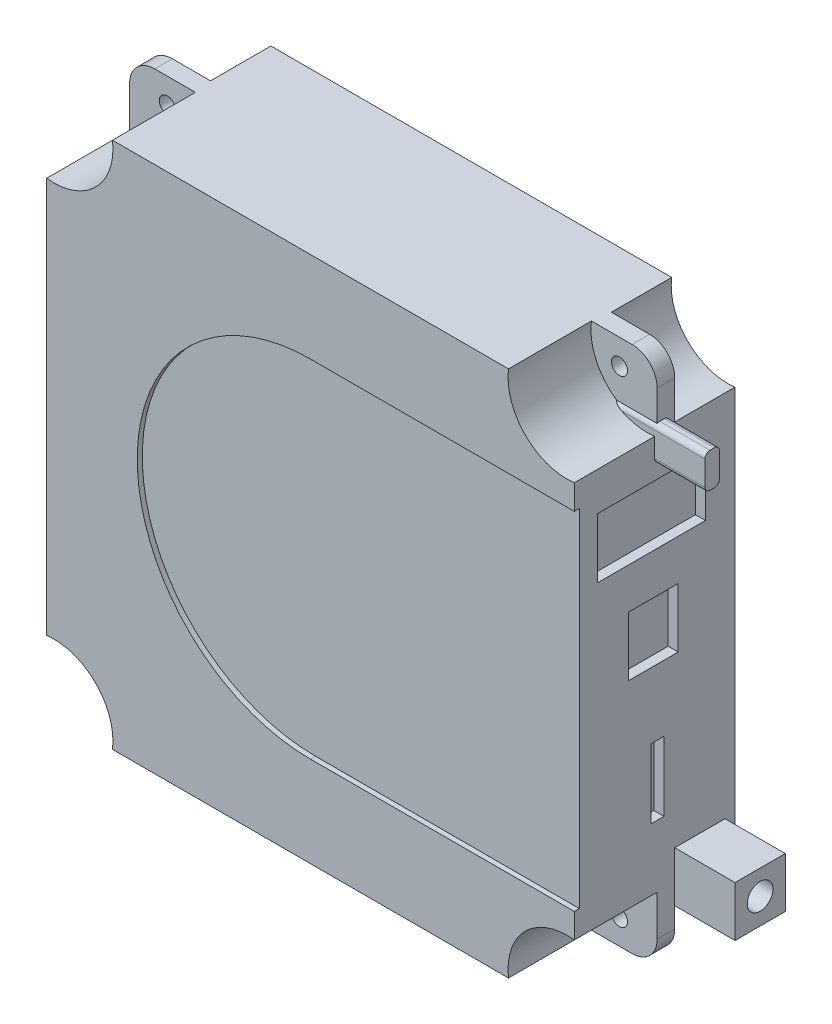
SolidWorks part; units mm, degrees
ref_plane "前视基准面" through (0, 0, 0) normal (0, 0, 1) x (1, 0, 0)
ref_plane "上视基准面" through (0, 0, 0) normal (0, 1, 0) x (1, 0, 0)
ref_plane "右视基准面" through (0, 0, 0) normal (1, 0, 0) x (0, 0, -1)
sketch "草图1" plane through (0, 0, 0) normal (0, 0, 1) x (1, 0, 0)
  line L1 (-47.5, -52.5) -> (47.5, -52.5)
  line L2 (-52.5, -47.5) -> (-52.5, 47.5)
  line L3 (-47.5, 52.5) -> (47.5, 52.5)
  line L4 (52.5, -47.5) -> (52.5, 47.5)
  line L5 (-52.5, -52.5) -> (52.5, 52.5) construction
  line L6 (-52.5, 52.5) -> (52.5, -52.5) construction
  line L7 (-45, -47.5) -> (45, -47.5)
  line L8 (-45, -47.5) -> (-45, 47.5)
  line L9 (-45, 47.5) -> (45, 47.5)
  line L10 (45, -47.5) -> (45, 47.5)
  line L11 (-45, -47.5) -> (45, 47.5) construction
  line L12 (-45, 47.5) -> (45, -47.5) construction
  circle A0 centre (-45, 47.5) radius 1.6
  circle A1 centre (45, 47.5) radius 1.6
  circle A2 centre (-45, -47.5) radius 1.6
  circle A3 centre (45, -47.5) radius 1.6
  arc A4 (52.5, -47.5) -> (47.5, -52.5) centre (47.5, -47.5) cw
  arc A5 (-47.5, -52.5) -> (-52.5, -47.5) centre (-47.5, -47.5) cw
  arc A6 (52.5, 47.5) -> (47.5, 52.5) centre (47.5, 47.5) ccw
  arc A7 (-52.5, 47.5) -> (-47.5, 52.5) centre (-47.5, 47.5) cw
  point P0 (0, 0)
  point P6 (0, 0)
  dimension "D5" = 5
  dimension "D1" = 105
  dimension "D2" = 105
  dimension "D3" = 90
  dimension "D4" = 95
extrude "凸台-拉伸1" add sketch "草图1" along normal blind 32 contours A7 L2 A5 L1 A4 L4 A6 L3 A3 L7 A2 L8 A0 L9 A1 L10 | A3 L10 A1 L9 A0 L8 A2 L7
sketch "草图2" plane through (52.5, 0, 0) normal (1, 0, 0) x (0, 0, -1)
  line L1 (-21.2339, 11.7062) -> (-11.3035, 11.7062)
  line L2 (-21.2339, 11.7062) -> (-21.2339, -0.111)
  line L3 (-21.2339, -0.111) -> (-11.3035, -0.111)
  line L4 (-11.3035, 11.7062) -> (-11.3035, -0.111)
  line L5 (-27.337, 31.7636) -> (-5.8873, 31.7636)
  line L6 (-27.337, 31.7636) -> (-27.337, 19.8471)
  line L7 (-27.337, 19.8471) -> (-5.8873, 19.8471)
  line L8 (-5.8873, 31.7636) -> (-5.8873, 19.8471)
  line L9 (-16.7269, -13.2121) -> (-14.145, -13.2121)
  line L10 (-16.7269, -13.2121) -> (-16.7269, -27.0154)
  line L11 (-16.7269, -27.0154) -> (-14.145, -27.0154)
  line L12 (-14.145, -13.2121) -> (-14.145, -27.0154)
extrude "切除-拉伸1" cut sketch "草图2" against normal blind 2
sketch "草图3" plane through (0, 0, 32) normal (0, 0, 1) x (1, 0, 0)
  circle A0 centre (-51.0355, 51.0355) radius 11.717
  arc A1 (-47.5, 52.5) -> (-52.5, 47.5) centre (-47.5, 47.5) ccw construction
  circle A2 centre (51.0355, 51.0355) radius 11.717
  circle A3 centre (51.0355, -51.0355) radius 11.717
  circle A4 centre (-51.0355, -51.0355) radius 11.717
  point P14 (0, 0)
  dimension "D1" = 4
extrude "切除-拉伸2" cut sketch "草图3" against normal blind 16.5
sketch "草图4" plane through (0, 0, 0) normal (0, 0, -1) x (-1, 0, 0)
  circle A0 centre (-51.0355, 51.0355) radius 11.2417
  arc A1 (-47.5, 52.5) -> (-52.5, 47.5) centre (-47.5, 47.5) ccw construction
  circle A2 centre (51.0355, 51.0355) radius 11.2417
  circle A3 centre (51.0355, -51.0355) radius 11.2417
  circle A4 centre (-51.0355, -51.0355) radius 11.2417
  point P14 (0, 0)
  dimension "D1" = 4
extrude "切除-拉伸3" cut sketch "草图4" against normal blind 12
sketch "草图5" plane through (0, 0, 32) normal (0, 0, 1) x (1, 0, 0)
  line L0 (0, 34.4797) -> (52.5, 34.4797)
  line L1 (52.5, -39.4104) -> (52.5, 39.4104) construction
  line L2 (52.5, 34.4797) -> (52.5, -34.4797)
  line L3 (52.5, -34.4797) -> (0, -34.4797)
  circle A0 centre (0, 0) radius 34.4797
  line M5 (52.5, -39.4104) -> (52.5, 39.4104)
extrude "切除-拉伸4" cut sketch "草图5" against normal blind 1 contours A0 | A0 L3 L0 M5
sketch "草图6" plane through (0, 0, 32) normal (0, 0, 1) x (1, 0, 0)
  line L0 (45, 47.5) -> (45, 41.5)
  line L1 (45, -47.5) -> (45, -43.5)
sketch "草图7" plane through (52.5, 0, 0) normal (1, 0, 0) x (0, 0, -1)
  line L1 (-12, -43.5) -> (-2, -43.5)
  line L2 (-12, -43.5) -> (-12, -33.5)
  line L3 (-12, -33.5) -> (-2, -33.5)
  line L4 (-2, -43.5) -> (-2, -33.5)
extrude "凸台-拉伸2" add sketch "草图7" along normal blind 25 from offset 13 offset against normal yes
sketch "草图8" plane through (64.5, 0, 0) normal (1, 0, 0) x (0, 0, -1)
  circle A0 centre (-7, -38.3811) radius 2.5652
extrude "切除-拉伸5" cut sketch "草图8" against normal blind 5
sketch "草图9" plane through (52.5, 0, 0) normal (1, 0, 0) x (0, 0, -1)
  line L1 (-15, 41.5) -> (-14.1082, 41.5)
  line L2 (-16, 40.5) -> (-16, 35.6076)
  line L3 (-15, 34.6076) -> (-14.1082, 34.6076)
  line L4 (-13.1082, 40.5) -> (-13.1082, 35.6076)
  arc A0 (-15, 34.6076) -> (-16, 35.6076) centre (-15, 35.6076) cw
  arc A1 (-14.1082, 34.6076) -> (-13.1082, 35.6076) centre (-14.1082, 35.6076) ccw
  arc A2 (-14.1082, 41.5) -> (-13.1082, 40.5) centre (-14.1082, 40.5) cw
  arc A3 (-15, 41.5) -> (-16, 40.5) centre (-15, 40.5) ccw
  point P14 (-32, 41.5)
  dimension "D1" = 1
extrude "凸台-拉伸3" add sketch "草图9" along normal mid plane 20
